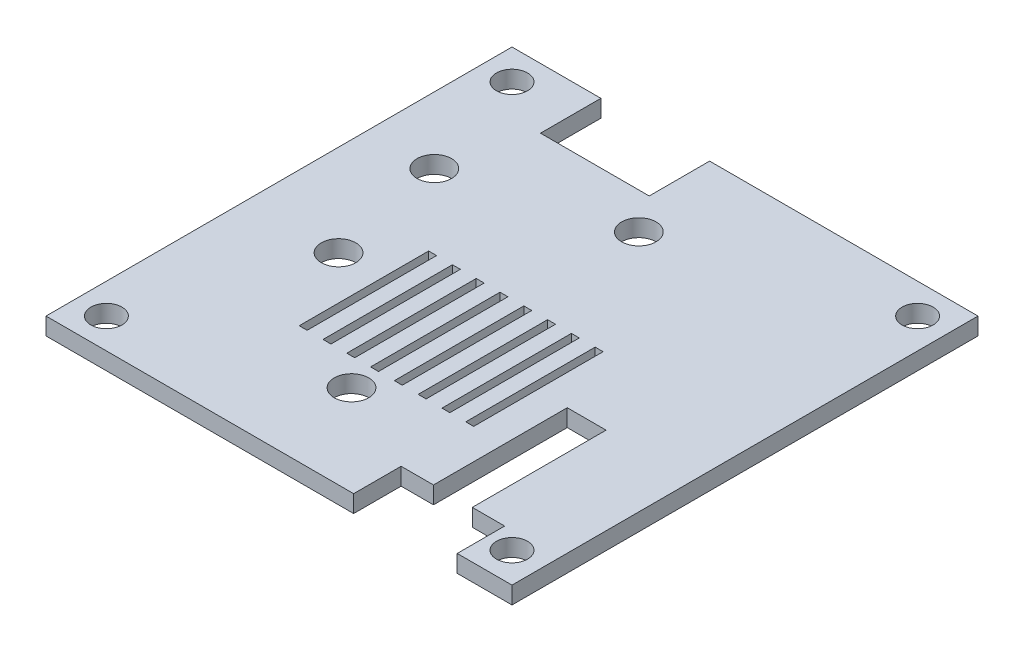
SolidWorks part; units mm, degrees
ref_plane "Front" through (0, 0, 0) normal (0, 0, 1) x (1, 0, 0)
ref_plane "Top" through (0, 0, 0) normal (0, 1, 0) x (1, 0, 0)
ref_plane "Right" through (0, 0, 0) normal (1, 0, 0) x (0, 0, -1)
sketch "草图3" plane through (0, 0, 0) normal (0, 1, 0) x (1, 0, 0)
  line L0 (16.9, -20) -> (20, -20)
  line L1 (-20, -20) -> (12.4, -20)
  line L2 (20, -20) -> (20, 20)
  line L3 (-27, 27) -> (-27, -27)
  line L4 (-27, -27) -> (27, -27)
  line L5 (27, -27) -> (27, 27)
  line L6 (27, 27) -> (-27, 27)
  line L7 (-8.6, 1.7) -> (-7.6812, 1.7)
  line L8 (-5.8437, 1.7) -> (-4.925, 1.7)
  line L9 (20.65, -20) -> (20, -20)
  line L10 (16.9, -6) -> (12.4, -6)
  line L11 (12.4, -6) -> (12.4, -19.5)
  line L12 (-10.4, 20) -> (-4.1, 20)
  line L13 (16.9, -6) -> (16.9, -19.5)
  line L14 (-20, 20) -> (-20, -20)
  line L15 (-3.0875, 1.7) -> (-2.1687, 1.7)
  line L16 (-0.3312, 1.7) -> (0.5875, 1.7)
  line L17 (2.425, 1.7) -> (3.3438, 1.7)
  line L18 (5.1813, 1.7) -> (6.1, 1.7)
  line L19 (8.8563, -13.3) -> (7.9375, -13.3)
  line L20 (8.65, -20) -> (8.65, -27)
  line L21 (-8.6, 1.7) -> (-8.6, -13.3)
  line L22 (-7.6812, -13.3) -> (-8.6, -13.3)
  line L23 (-8.6, -13.3) -> (-8.6029, -13.3589)
  line L24 (-10.4375, -13.3) -> (-11.3562, -13.3)
  line L25 (-10.4375, 1.7) -> (-11.3562, 1.7)
  line L26 (6.1, 1.7) -> (6.1, -13.3)
  line L27 (-4.925, -13.3) -> (-4.925, 1.7)
  line L28 (-11.3562, -13.3) -> (-11.3562, 1.7)
  line L29 (-3.0875, -13.3) -> (-3.0875, 1.7)
  line L30 (-10.4375, -13.3) -> (-10.4375, 1.7)
  line L31 (-2.1687, -13.3) -> (-2.1687, 1.7)
  line L32 (8.8563, 1.7) -> (7.9375, 1.7)
  line L33 (-5.8437, -13.3) -> (-5.8437, 1.7)
  line L34 (8.8563, -13.3) -> (8.8563, 1.7)
  line L35 (-7.6812, -13.3) -> (-7.6812, 1.7)
  line L36 (-0.3312, -13.3) -> (-0.3312, 1.7)
  line L37 (0.5875, -13.3) -> (0.5875, 1.7)
  line L38 (5.1813, -13.3) -> (6.1, -13.3)
  line L39 (2.425, -13.3) -> (2.425, 1.7)
  line L40 (3.3438, -13.3) -> (3.3438, 1.7)
  line L41 (2.425, -13.3) -> (3.3438, -13.3)
  line L42 (5.1813, -13.3) -> (5.1813, 1.7)
  line L43 (-0.3312, -13.3) -> (0.5875, -13.3)
  line L44 (-3.0875, -13.3) -> (-2.1687, -13.3)
  line L45 (-5.8437, -13.3) -> (-4.925, -13.3)
  line L46 (7.9375, -13.3) -> (7.9375, 1.7)
  line L47 (20.65, -20) -> (20.65, -27)
  line L48 (12.4, -19.5) -> (12.4, -20)
  line L49 (16.9, -19.5) -> (16.9, -20)
  line L50 (-20, -20) -> (20, -20) construction
  line L51 (-20, 20) -> (20, 20)
  line L52 (-16.7, 20) -> (-10.4, 20)
  line L53 (20, 20) -> (-20, 20) construction
  line L54 (-16.7, 20) -> (-16.7, 27)
  line L55 (-4.1, 20) -> (-4.1, 27)
  line L56 (12.4, -20) -> (12.4, -21.5)
  line L57 (8.65, -21.5) -> (20.65, -21.5)
  line L58 (16.9, -20) -> (16.9, -21.5)
  circle A0 centre (-23.5, -23.5) radius 1.8
  circle A1 centre (23.5, -23.5) radius 1.8
  circle A2 centre (-23.5, 23.5) radius 1.8
  circle A3 centre (23.5, 23.5) radius 1.8
  circle A4 centre (-2.1, -16.5) radius 2
  circle A5 centre (-16.4, -3.7) radius 2
  circle A6 centre (-19.3, 10.3) radius 2
  circle A7 centre (-1.1, 15.8) radius 2
  point P0 (0, 0)
  point P61 (-10.8969, 1.7)
  dimension "D1" = 7
extrude "凸台-拉伸2" add sketch "草图3" along normal blind 2
